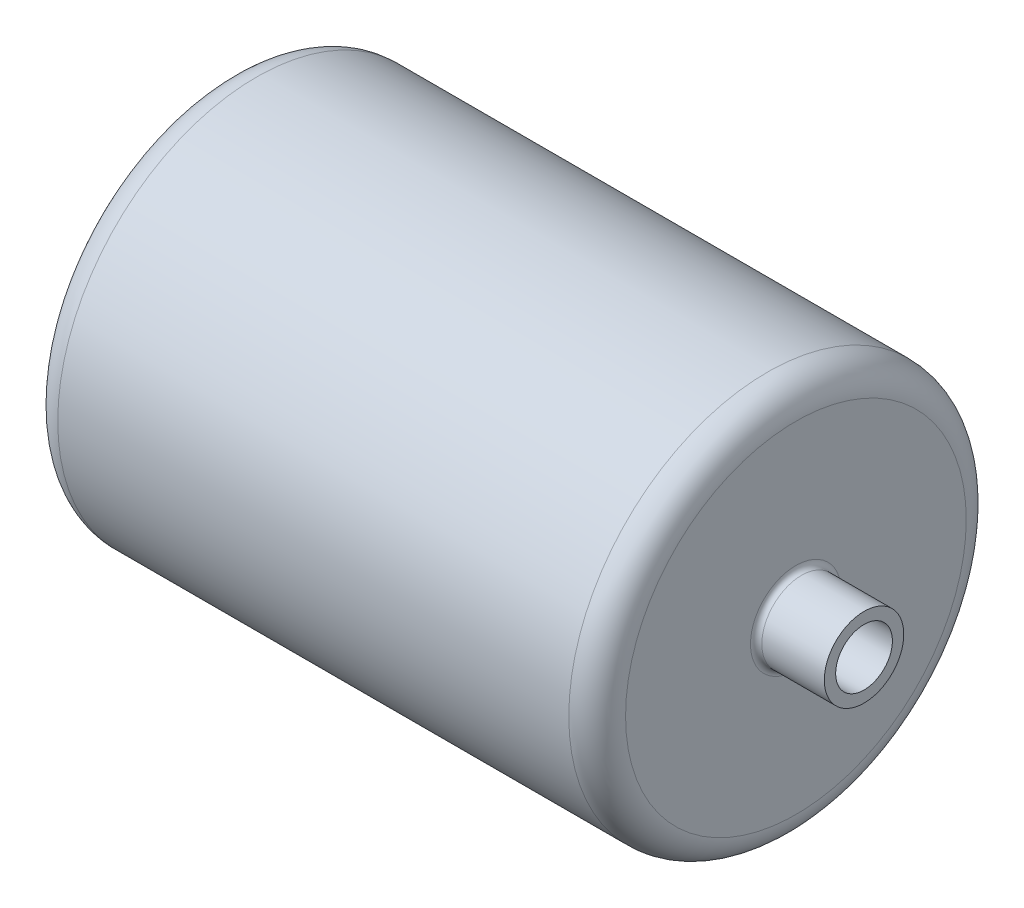
SolidWorks part; units mm, degrees
ref_plane "Front Plane" through (0, 0, 0) normal (0, 0, 1) x (1, 0, 0)
ref_plane "Top Plane" through (0, 0, 0) normal (0, 1, 0) x (1, 0, 0)
ref_plane "Right Plane" through (0, 0, 0) normal (1, 0, 0) x (0, 0, -1)
sketch "Sketch1" plane through (0, 0, 0) normal (0, 0, 1) x (1, 0, 0)
  line L0 (-225, 175) -> (225, 175)
  line L1 (-250, 150) -> (-250, 0)
  line L2 (-225, 0) -> (-225, 137.5)
  line L3 (-212.5, 150) -> (212.5, 150)
  line L4 (225, 137.5) -> (225, 25)
  line L5 (225, 25) -> (310, 25)
  line L6 (310, 25) -> (310, 35)
  line L7 (310, 35) -> (250, 35)
  line L8 (250, 35) -> (250, 150)
  line L9 (-225, 0) -> (-250, 0)
  line L10 (-162.2867, 0) -> (219.9588, 0) construction
  arc A0 (-225, 137.5) -> (-212.5, 150) centre (-212.5, 137.5) cw
  arc A1 (225, 137.5) -> (212.5, 150) centre (212.5, 137.5) ccw
  arc A2 (250, 150) -> (225, 175) centre (225, 150) ccw
  arc A3 (-250, 150) -> (-225, 175) centre (-225, 150) cw
  point P19 (250, 175)
  point P22 (-250, 175)
  dimension "D11" = 12.5
  dimension "D12" = 12.5
  dimension "D13" = 25
  dimension "D14" = 150
  dimension "D2" = 25
  dimension "D3" = 25
  dimension "D4" = 500
  dimension "D5" = 35
  dimension "D6" = 25
  dimension "D7" = 85
  dimension "D8" = 250
  dimension "D9" = 150
  dimension "D10" = 175
revolve "Revolve1" add sketch "Sketch1" angle 360 about L10
sketch "Sketch4" plane through (0, 0, 0) normal (1, 0, 0) x (0, 0, -1)
  line L0 (0, 190.4729) -> (0, -189.774)
extrude "Half-Model of Cylinder" [suppressed] cut sketch "Sketch4" against normal through all and the other way through all flip side to cut
fillet "Pipe Connector Fillet" radius 5 1 edges at (250, 0, 35)
